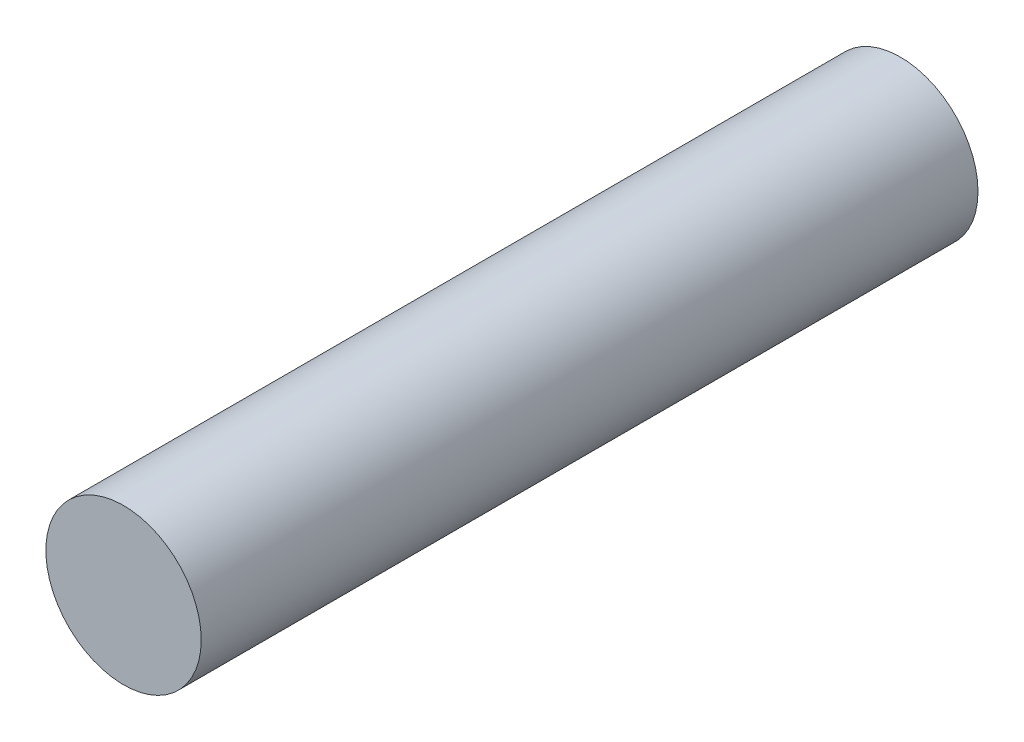
SolidWorks part; units mm, degrees
ref_plane "Front Plane" through (0, 0, 0) normal (0, 0, 1) x (1, 0, 0)
ref_plane "Top Plane" through (0, 0, 0) normal (0, 1, 0) x (1, 0, 0)
ref_plane "Right Plane" through (0, 0, 0) normal (1, 0, 0) x (0, 0, -1)
sketch "Sketch1" plane through (0, 0, 0) normal (0, 0, 1) x (1, 0, 0)
  circle A0 centre (0.8847, 2.5675) radius 1.5
  dimension "D1" = 3
extrude "Boss-Extrude1" add sketch "Sketch1" along normal blind 15
